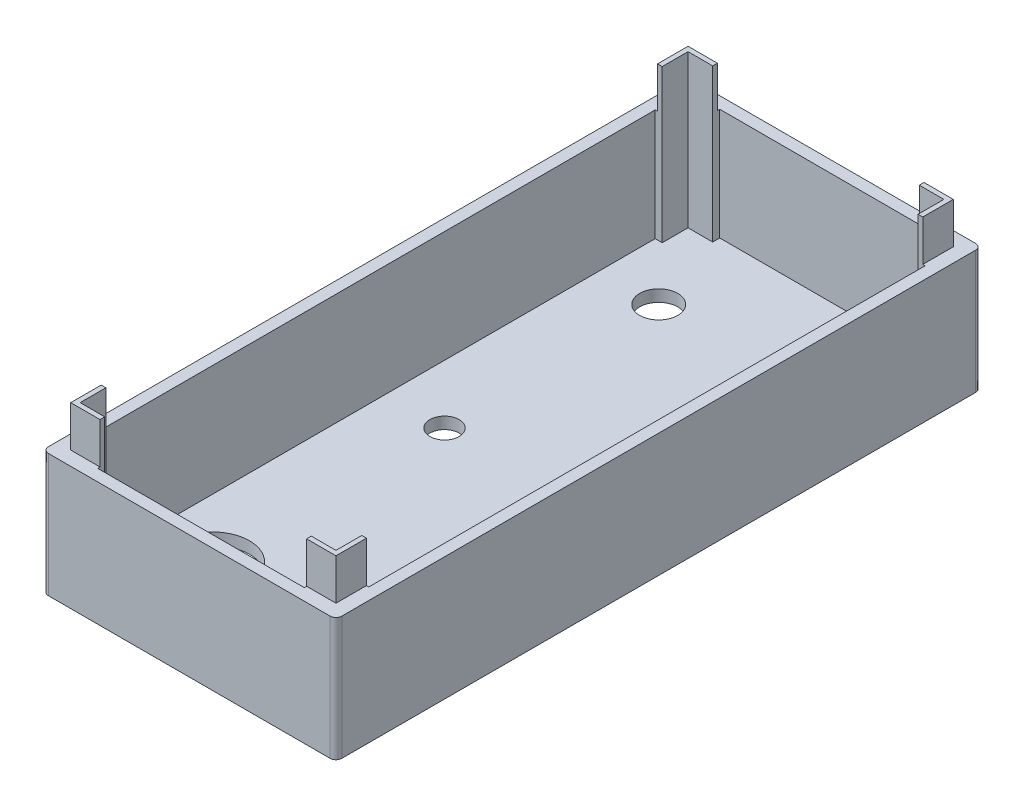
SolidWorks part; units mm, degrees
ref_plane "Front Plane" through (0, 0, 0) normal (0, 0, 1) x (1, 0, 0)
ref_plane "Top Plane" through (0, 0, 0) normal (0, 1, 0) x (1, 0, 0)
ref_plane "Right Plane" through (0, 0, 0) normal (1, 0, 0) x (0, 0, -1)
sketch "Sketch1" plane through (0, 0, 0) normal (0, 1, 0) x (1, 0, 0)
  line L1 (-77.0226, 53.0801) -> (-27.0226, 53.0801)
  line L2 (-77.0226, 53.0801) -> (-77.0226, -56.9199)
  line L3 (-77.0226, -56.9199) -> (-27.0226, -56.9199)
  line L4 (-27.0226, 53.0801) -> (-27.0226, -56.9199)
  dimension "D1" = 110
  dimension "D2" = 50
extrude "Boss-Extrude1" add sketch "Sketch1" along normal blind 2
sketch "Sketch2" plane through (0, 2, 0) normal (0, 1, 0) x (1, 0, 0)
  line L0 (-75.0226, 51.0801) -> (-75.0226, -54.9199)
  line L1 (-77.0226, 53.0801) -> (-27.0226, 53.0801)
  line L2 (-77.0226, 53.0801) -> (-77.0226, -56.9199)
  line L3 (-77.0226, -56.9199) -> (-27.0226, -56.9199)
  line L4 (-27.0226, 53.0801) -> (-27.0226, -56.9199)
  line L5 (-75.0226, -54.9199) -> (-29.0226, -54.9199)
  line L6 (-29.0226, 51.0801) -> (-29.0226, -54.9199)
  line L7 (-75.0226, 51.0801) -> (-29.0226, 51.0801)
  dimension "D1" = 2
extrude "Boss-Extrude3" add sketch "Sketch2" along normal blind 11
sketch "Sketch3" plane through (0, 2, 0) normal (0, 1, 0) x (1, 0, 0)
  circle A0 centre (-31.0226, 42.3801) radius 1.2
  circle A1 centre (-31.0226, -52.9199) radius 1.2
  circle A2 centre (-56.3226, 42.3801) radius 1.2
  circle A3 centre (-56.3226, -52.9199) radius 1.2
extrude "Boss-Extrude4" add sketch "Sketch3" along normal blind 11
sketch "Sketch4" plane through (0, 13, 0) normal (0, 1, 0) x (1, 0, 0)
  line L8 (-26.0226, 54.0801) -> (-78.0226, 54.0801)
  line L9 (-78.0226, 54.0801) -> (-78.0226, -57.9199)
  line L10 (-78.0226, -57.9199) -> (-26.0226, -57.9199)
  line L11 (-26.0226, -57.9199) -> (-26.0226, 54.0801)
  line L12 (-26.0226, 54.0801) -> (-78.0226, 54.0801)
  line L13 (-78.0226, 54.0801) -> (-78.0226, -57.9199)
  line L14 (-78.0226, -57.9199) -> (-26.0226, -57.9199)
  line L15 (-26.0226, -57.9199) -> (-26.0226, 54.0801)
  dimension "D1" = 3
extrude "Extrude-Thin1" add sketch "Sketch4" against normal blind 13 thin thin type one direction reverse wall 1
fillet "Fillet2" radius 2 4 edges at (-78.0226, 6.5, -54.0801) (-26.0226, 6.5, -54.0801) (-26.0226, 6.5, 57.9199) (-78.0226, 6.5, 57.9199)
sketch "Sketch5" plane through (0, 13, 0) normal (0, 1, 0) x (1, 0, 0)
  line L8 (-28.0226, 52.8801) -> (-76.0226, 52.8801)
  line L9 (-76.8226, 52.0801) -> (-76.8226, -55.9199)
  line L10 (-76.0226, -56.7199) -> (-28.0226, -56.7199)
  line L11 (-27.2226, -55.9199) -> (-27.2226, 52.0801)
  line L12 (-28.0226, 52.8801) -> (-76.0226, 52.8801)
  line L13 (-76.8226, 52.0801) -> (-76.8226, -55.9199)
  line L14 (-76.0226, -56.7199) -> (-28.0226, -56.7199)
  line L15 (-27.2226, -55.9199) -> (-27.2226, 52.0801)
  arc A8 (-76.0226, 52.8801) -> (-76.8226, 52.0801) centre (-76.0226, 52.0801) ccw
  arc A9 (-76.8226, -55.9199) -> (-76.0226, -56.7199) centre (-76.0226, -55.9199) ccw
  arc A10 (-28.0226, -56.7199) -> (-27.2226, -55.9199) centre (-28.0226, -55.9199) ccw
  arc A11 (-27.2226, 52.0801) -> (-28.0226, 52.8801) centre (-28.0226, 52.0801) ccw
  arc A12 (-76.0226, 52.8801) -> (-76.8226, 52.0801) centre (-76.0226, 52.0801) ccw
  arc A13 (-76.8226, -55.9199) -> (-76.0226, -56.7199) centre (-76.0226, -55.9199) ccw
  arc A14 (-28.0226, -56.7199) -> (-27.2226, -55.9199) centre (-28.0226, -55.9199) ccw
  arc A15 (-27.2226, 52.0801) -> (-28.0226, 52.8801) centre (-28.0226, 52.0801) ccw
  dimension "D1" = 1.2
extrude "Extrude-Thin3" add sketch "Sketch5" along normal blind 3 thin
sketch "Sketch6" plane through (0, 2, 0) normal (0, 1, 0) x (1, 0, 0)
  circle A0 centre (-56.3226, -52.9199) radius 1.8
  circle A1 centre (-31.0226, -52.9199) radius 1.8
  circle A2 centre (-56.3226, 42.3801) radius 1.8
  circle A3 centre (-31.0226, 42.3801) radius 1.8
extrude "Boss-Extrude5" add sketch "Sketch6" along normal blind 2.8
sketch "Sketch7" plane through (0, 2, 0) normal (0, 1, 0) x (1, 0, 0)
  line L0 (-31.0226, -52.9199) -> (-31.0226, -48.6199)
  line L1 (-31.0226, -48.6199) -> (-18.3371, -48.6199)
sketch "Sketch8" plane through (-26.0226, 0, 0) normal (1, 0, 0) x (0, 0, -1)
  line L0 (-52.9199, 2) -> (-48.6199, 2) construction
  line L2 (-48.6199, 2) -> (-40.6199, 2)
  line L3 (-48.6199, 2) -> (-48.6199, 5.6)
  line L4 (-48.6199, 5.6) -> (-40.6199, 5.6)
  line L5 (-40.6199, 2) -> (-40.6199, 5.6)
  dimension "D1" = 8
  dimension "D2" = 3.6
extrude "Cut-Extrude2" cut sketch "Sketch8" against normal blind 12.8
sketch "Sketch11" plane through (-78.0226, 0, 0) normal (-1, 0, 0) x (0, 0, 1)
  line L0 (-51.0801, 2) -> (54.9199, 2) construction
  line L1 (-50.0801, 7.8) -> (-36.9801, 7.8)
  line L2 (-50.0801, 7.8) -> (-50.0801, 2)
  line L3 (-50.0801, 2) -> (-36.9801, 2)
  line L4 (-36.9801, 7.8) -> (-36.9801, 2)
  line L5 (-51.0801, 13) -> (-51.0801, 2) construction
  dimension "D1" = 5.8
  dimension "D2" = 13.1
  dimension "D3" = 0
  dimension "D4" = 1
extrude "Cut-Extrude5" cut sketch "Sketch11" against normal blind 3
sketch "Sketch12" plane through (0, 0, 57.9199) normal (0, 0, 1) x (1, 0, 0)
  line L0 (-78.0226, 0) -> (-78.0226, 16) construction
  line L1 (-88.0226, 10.3909) -> (-18.0226, 10.3909)
  line L2 (-88.0226, 10.3909) -> (-88.0226, 20.3641)
  line L3 (-88.0226, 20.3641) -> (-18.0226, 20.3641)
  line L4 (-18.0226, 10.3909) -> (-18.0226, 20.3641)
  dimension "D1" = 70
  dimension "D2" = 10
extrude "Cut-Extrude6" cut sketch "Sketch12" against normal blind 130
sketch "Sketch13" plane through (0, 2, 0) normal (0, 1, 0) x (1, 0, 0)
  line L1 (-75.0226, 51.0801) -> (-29.0226, 51.0801)
  line L2 (-75.0226, 51.0801) -> (-75.0226, -54.9199)
  line L3 (-75.0226, -54.9199) -> (-29.0226, -54.9199)
  line L4 (-29.0226, 51.0801) -> (-29.0226, -54.9199)
extrude "Cut-Extrude7" cut sketch "Sketch13" along normal blind 130
sketch "Sketch15" plane through (0, 10.3909, 0) normal (0, 1, 0) x (1, 0, 0)
  line L8 (-76.0226, -57.9199) -> (-28.0226, -57.9199)
  line L9 (-26.0226, -55.9199) -> (-26.0226, 52.0801)
  line L10 (-28.0226, 54.0801) -> (-76.0226, 54.0801)
  line L11 (-78.0226, 52.0801) -> (-78.0226, -55.9199)
  line L12 (-76.0226, -57.9199) -> (-28.0226, -57.9199)
  line L13 (-26.0226, -55.9199) -> (-26.0226, 52.0801)
  line L14 (-28.0226, 54.0801) -> (-76.0226, 54.0801)
  line L15 (-78.0226, 52.0801) -> (-78.0226, -55.9199)
  line L20 (-75.0226, -54.9199) -> (-29.0226, -54.9199)
  line L21 (-29.0226, -54.9199) -> (-29.0226, 51.0801)
  line L22 (-29.0226, 51.0801) -> (-75.0226, 51.0801)
  line L23 (-75.0226, 51.0801) -> (-75.0226, -54.9199)
  line L24 (-75.0226, -54.9199) -> (-29.0226, -54.9199)
  line L25 (-29.0226, -54.9199) -> (-29.0226, 51.0801)
  line L26 (-29.0226, 51.0801) -> (-75.0226, 51.0801)
  line L27 (-75.0226, 51.0801) -> (-75.0226, -54.9199)
  arc A8 (-78.0226, -55.9199) -> (-76.0226, -57.9199) centre (-76.0226, -55.9199) ccw
  arc A9 (-28.0226, -57.9199) -> (-26.0226, -55.9199) centre (-28.0226, -55.9199) ccw
  arc A10 (-26.0226, 52.0801) -> (-28.0226, 54.0801) centre (-28.0226, 52.0801) ccw
  arc A11 (-76.0226, 54.0801) -> (-78.0226, 52.0801) centre (-76.0226, 52.0801) ccw
  arc A12 (-78.0226, -55.9199) -> (-76.0226, -57.9199) centre (-76.0226, -55.9199) ccw
  arc A13 (-28.0226, -57.9199) -> (-26.0226, -55.9199) centre (-28.0226, -55.9199) ccw
  arc A14 (-26.0226, 52.0801) -> (-28.0226, 54.0801) centre (-28.0226, 52.0801) ccw
  arc A15 (-76.0226, 54.0801) -> (-78.0226, 52.0801) centre (-76.0226, 52.0801) ccw
  dimension "D1" = 0
  dimension "D2" = 0
extrude "Boss-Extrude6" add sketch "Sketch15" along normal blind 60
sketch "Sketch16" plane through (0, 0, 57.9199) normal (0, 0, 1) x (1, 0, 0)
  line L0 (-76.0226, 0) -> (-28.0226, 0) construction
  line L1 (-84.3923, 79.1661) -> (-12.6524, 79.1661)
  line L2 (-84.3923, 79.1661) -> (-84.3923, 24)
  line L3 (-84.3923, 24) -> (-12.6524, 24)
  line L4 (-12.6524, 79.1661) -> (-12.6524, 24)
  dimension "D1" = 24
extrude "Cut-Extrude8" cut sketch "Sketch16" against normal blind 130
sketch "Sketch17" plane through (0, 24, 0) normal (0, 1, 0) x (1, 0, 0)
  line L16 (-76.2226, -56.1199) -> (-27.8226, -56.1199)
  line L17 (-27.8226, -56.1199) -> (-27.8226, 52.2801)
  line L18 (-27.8226, 52.2801) -> (-76.2226, 52.2801)
  line L19 (-76.2226, 52.2801) -> (-76.2226, -56.1199)
  line L20 (-76.2226, -56.1199) -> (-27.8226, -56.1199)
  line L21 (-27.8226, -56.1199) -> (-27.8226, 52.2801)
  line L22 (-27.8226, 52.2801) -> (-76.2226, 52.2801)
  line L23 (-76.2226, 52.2801) -> (-76.2226, -56.1199)
  dimension "D1" = 1.2
extrude "Cut-Extrude-Thin1" cut sketch "Sketch17" against normal blind 3 thin
sketch "Sketch18" plane through (0, 7.8, 0) normal (0, -1, 0) x (1, 0, 0)
  line L1 (-75.0226, -36.9801) -> (-78.0226, -36.9801)
  line L2 (-75.0226, -36.9801) -> (-75.0226, -50.0801)
  line L3 (-75.0226, -50.0801) -> (-78.0226, -50.0801)
  line L4 (-78.0226, -36.9801) -> (-78.0226, -50.0801)
extrude "Boss-Extrude7" add sketch "Sketch18" along normal blind 7
sketch "Sketch19" plane through (0, 5.6, 0) normal (0, -1, 0) x (1, 0, 0)
  line L1 (-29.0226, 48.6199) -> (-26.0226, 48.6199)
  line L2 (-29.0226, 48.6199) -> (-29.0226, 40.6199)
  line L3 (-29.0226, 40.6199) -> (-26.0226, 40.6199)
  line L4 (-26.0226, 48.6199) -> (-26.0226, 40.6199)
extrude "Boss-Extrude8" add sketch "Sketch19" along normal blind 4.5
sketch "Sketch20" plane through (0, 2, 0) normal (0, 1, 0) x (1, 0, 0)
  line L4 (-29.0226, 51.0801) -> (-75.0226, 51.0801) construction
  line L5 (-75.0226, -54.9199) -> (-29.0226, -54.9199) construction
  circle A0 centre (-65.0226, -39.9199) radius 6
  circle A1 centre (-65.0226, 36.0801) radius 3
  dimension "D4" = 15
  dimension "D5" = 15
extrude "Cut-Extrude9" cut sketch "Sketch20" against normal blind 4.5
sketch "Sketch23" plane through (0, 21, 0) normal (0, 1, 0) x (1, 0, 0)
  line L8 (-76.0226, -56.9199) -> (-28.0226, -56.9199)
  line L9 (-27.0226, -55.9199) -> (-27.0226, 52.0801)
  line L10 (-28.0226, 53.0801) -> (-76.0226, 53.0801)
  line L11 (-77.0226, 52.0801) -> (-77.0226, -55.9199)
  line L12 (-76.0226, -56.9199) -> (-28.0226, -56.9199)
  line L13 (-27.0226, -55.9199) -> (-27.0226, 52.0801)
  line L14 (-28.0226, 53.0801) -> (-76.0226, 53.0801)
  line L15 (-77.0226, 52.0801) -> (-77.0226, -55.9199)
  arc A8 (-77.0226, -55.9199) -> (-76.0226, -56.9199) centre (-76.0226, -55.9199) ccw
  arc A9 (-28.0226, -56.9199) -> (-27.0226, -55.9199) centre (-28.0226, -55.9199) ccw
  arc A10 (-27.0226, 52.0801) -> (-28.0226, 53.0801) centre (-28.0226, 52.0801) ccw
  arc A11 (-76.0226, 53.0801) -> (-77.0226, 52.0801) centre (-76.0226, 52.0801) ccw
  arc A12 (-77.0226, -55.9199) -> (-76.0226, -56.9199) centre (-76.0226, -55.9199) ccw
  arc A13 (-28.0226, -56.9199) -> (-27.0226, -55.9199) centre (-28.0226, -55.9199) ccw
  arc A14 (-27.0226, 52.0801) -> (-28.0226, 53.0801) centre (-28.0226, 52.0801) ccw
  arc A15 (-76.0226, 53.0801) -> (-77.0226, 52.0801) centre (-76.0226, 52.0801) ccw
  dimension "D1" = 1
extrude "Cut-Extrude-Thin3" cut sketch "Sketch23" against normal blind 80 thin
sketch "Sketch24" plane through (0, 0, 56.1199) normal (0, 0, 1) x (1, 0, 0)
  line L1 (-76.2226, 24) -> (-27.8226, 24)
  line L2 (-76.2226, 24) -> (-76.2226, 21)
  line L3 (-76.2226, 21) -> (-27.8226, 21)
  line L4 (-27.8226, 24) -> (-27.8226, 21)
extrude "Cut-Extrude10" cut sketch "Sketch24" against normal blind 140
sketch "Sketch26" plane through (0, 2, 0) normal (0, 1, 0) x (1, 0, 0)
  line L8 (-30.2226, -53.7199) -> (-30.2226, 49.8801)
  line L9 (-30.2226, 49.8801) -> (-73.8226, 49.8801)
  line L10 (-73.8226, 49.8801) -> (-73.8226, -53.7199)
  line L11 (-73.8226, -53.7199) -> (-30.2226, -53.7199)
  line L12 (-30.2226, -53.7199) -> (-30.2226, 49.8801)
  line L13 (-30.2226, 49.8801) -> (-73.8226, 49.8801)
  line L14 (-73.8226, 49.8801) -> (-73.8226, -53.7199)
  line L15 (-73.8226, -53.7199) -> (-30.2226, -53.7199)
  dimension "D1" = 1.2
extrude "Extrude-Thin5" add sketch "Sketch26" along normal blind 26 thin
sketch "Sketch27" plane through (0, 28, 0) normal (0, 1, 0) x (1, 0, 0)
  line L8 (-74.6226, -54.5199) -> (-29.4226, -54.5199)
  line L9 (-29.4226, -54.5199) -> (-29.4226, 50.6801)
  line L10 (-29.4226, 50.6801) -> (-74.6226, 50.6801)
  line L11 (-74.6226, 50.6801) -> (-74.6226, -54.5199)
  line L12 (-74.6226, -54.5199) -> (-29.4226, -54.5199)
  line L13 (-29.4226, -54.5199) -> (-29.4226, 50.6801)
  line L14 (-29.4226, 50.6801) -> (-74.6226, 50.6801)
  line L15 (-74.6226, 50.6801) -> (-74.6226, -54.5199)
  dimension "D1" = 0.4
extrude "Cut-Extrude-Thin4" cut sketch "Sketch27" against normal blind 7 thin
sketch "Sketch28" plane through (-29.4226, 0, 0) normal (1, 0, 0) x (0, 0, -1)
  line L0 (-54.5199, 28) -> (50.6801, 28) construction
  line L1 (-49.3199, 28) -> (45.4801, 28)
  line L2 (-49.3199, 28) -> (-49.3199, 21)
  line L3 (-49.3199, 21) -> (45.4801, 21)
  line L4 (45.4801, 28) -> (45.4801, 21)
  line L5 (-54.5199, 21) -> (50.6801, 21) construction
  line L6 (50.6801, 21) -> (50.6801, 28) construction
  line L7 (-54.5199, 21) -> (-54.5199, 28) construction
  dimension "D1" = 5.2
  dimension "D2" = 5.2
extrude "Cut-Extrude11" cut sketch "Sketch28" against normal blind 87 and the other way blind 7
sketch "Sketch29" plane through (0, 0, 54.5199) normal (0, 0, 1) x (1, 0, 0)
  line L0 (-74.6226, 28) -> (-29.4226, 28) construction
  line L1 (-34.4226, 28) -> (-69.6226, 28)
  line L2 (-34.4226, 28) -> (-34.4226, 21)
  line L3 (-34.4226, 21) -> (-69.6226, 21)
  line L4 (-69.6226, 28) -> (-69.6226, 21)
  line L5 (-76.0226, 21) -> (-28.0226, 21) construction
  line L6 (-74.6226, 21) -> (-74.6226, 28) construction
  line L7 (-29.4226, 21) -> (-29.4226, 28) construction
  dimension "D1" = 5
  dimension "D2" = 5
extrude "Cut-Extrude12" cut sketch "Sketch29" against normal blind 137 and the other way blind 87
sketch "Sketch30" plane through (0, 21, 0) normal (0, 1, 0) x (1, 0, 0)
  line L0 (-73.8226, 45.4801) -> (-74.6226, 45.4801) construction
  line L1 (-75.0226, -49.3199) -> (-73.8226, -49.3199)
  line L2 (-75.0226, -49.3199) -> (-75.0226, 45.4801)
  line L3 (-75.0226, 45.4801) -> (-73.8226, 45.4801)
  line L4 (-73.8226, -49.3199) -> (-73.8226, 45.4801)
  line L5 (-73.8226, -49.3199) -> (-74.6226, -49.3199) construction
  line L6 (-73.8226, 45.4801) -> (-73.8226, -49.3199) construction
  line L7 (-34.4226, -54.5199) -> (-34.4226, -53.7199) construction
  line L8 (-69.6226, -53.7199) -> (-34.4226, -53.7199)
  line L9 (-69.6226, -53.7199) -> (-69.6226, -54.9199)
  line L10 (-69.6226, -54.9199) -> (-34.4226, -54.9199)
  line L11 (-34.4226, -53.7199) -> (-34.4226, -54.9199)
  line L12 (-69.6226, -54.5199) -> (-69.6226, -53.7199) construction
  line L13 (-73.8226, -53.7199) -> (-30.2226, -53.7199) construction
  line L14 (-29.4226, 45.4801) -> (-30.2226, 45.4801) construction
  line L15 (-30.2226, -49.3199) -> (-29.0226, -49.3199)
  line L16 (-30.2226, -49.3199) -> (-30.2226, 45.4801)
  line L17 (-30.2226, 45.4801) -> (-29.0226, 45.4801)
  line L18 (-29.0226, -49.3199) -> (-29.0226, 45.4801)
  line L19 (-29.4226, -49.3199) -> (-30.2226, -49.3199) construction
  line L20 (-30.2226, -53.7199) -> (-30.2226, 49.8801) construction
  line L21 (-69.6226, 49.8801) -> (-69.6226, 50.6801) construction
  line L22 (-69.6226, 51.0801) -> (-34.4226, 51.0801)
  line L23 (-69.6226, 51.0801) -> (-69.6226, 49.8801)
  line L24 (-69.6226, 49.8801) -> (-34.4226, 49.8801)
  line L25 (-34.4226, 51.0801) -> (-34.4226, 49.8801)
  line L26 (-34.4226, 49.8801) -> (-34.4226, 50.6801) construction
  line L27 (-34.4226, 49.8801) -> (-69.6226, 49.8801) construction
  dimension "D1" = 1.2
  dimension "D2" = 0
  dimension "D3" = 0
  dimension "D4" = 0
  dimension "D5" = 1.2
  dimension "D6" = 0
  dimension "D7" = 0
  dimension "D8" = 0
  dimension "D9" = 1.2
  dimension "D10" = 0
  dimension "D11" = 0
  dimension "D12" = 0
  dimension "D13" = 1.2
  dimension "D14" = 0
  dimension "D15" = 0
  dimension "D16" = 0
extrude "Cut-Extrude13" cut sketch "Sketch30" along direction (0, 1, 0) on the side against the normal up to surface (19 mm away)
sketch "Sketch31" plane through (0, 2, 0) normal (0, 1, 0) x (1, 0, 0)
  circle A0 centre (-65.0226, -39.9199) radius 6.25
extrude "Cut-Extrude14" cut sketch "Sketch31" against normal blind 10 and the other way blind 10
sketch "Sketch32" plane through (0, 2, 0) normal (0, 1, 0) x (1, 0, 0)
  circle A0 centre (-65.0226, 36.0801) radius 3.25
extrude "Cut-Extrude17" cut sketch "Sketch32" against normal blind 10
sketch "Sketch35" plane through (0, 2, 0) normal (0, 1, 0) x (1, 0, 0)
  circle A2 centre (-65.0226, -0.4199) radius 2.5
extrude "Cut-Extrude18" cut sketch "Sketch35" against normal blind 10 and the other way blind 10
